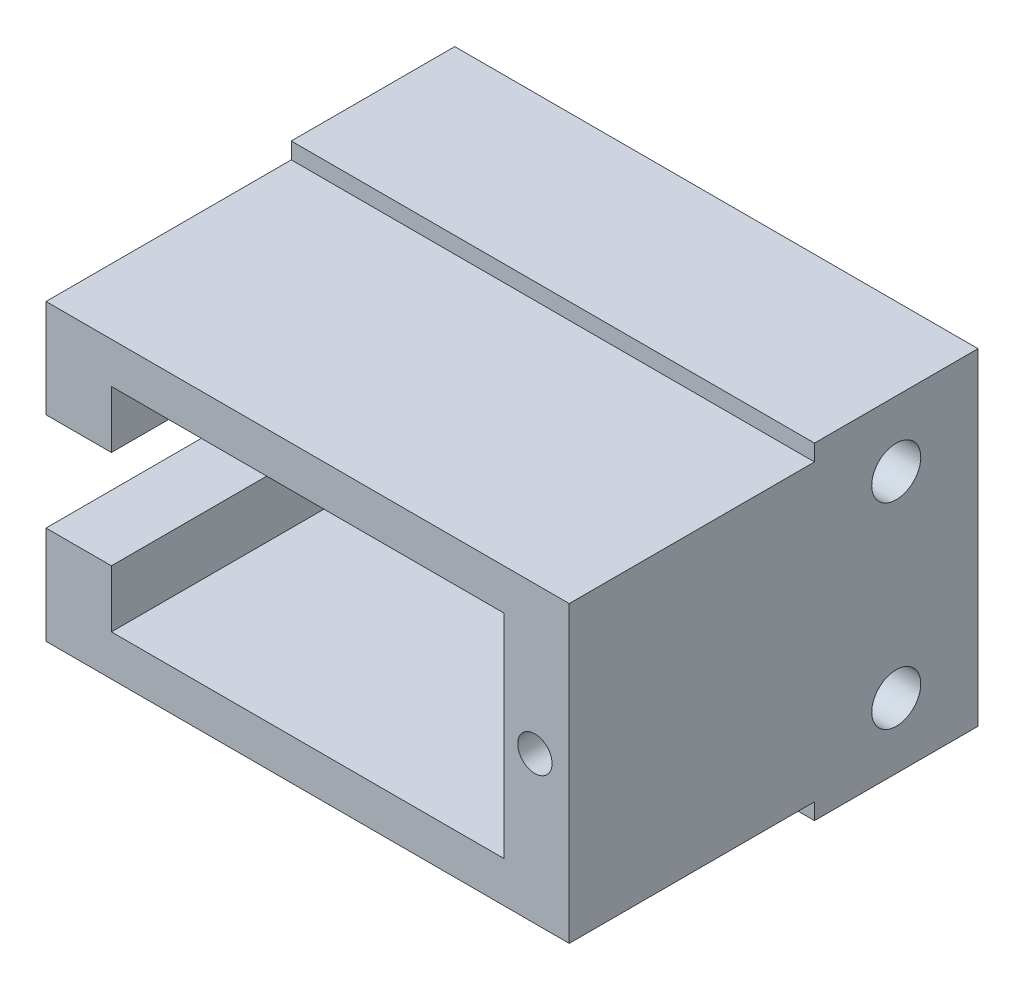
SolidWorks part; units mm, degrees
ref_plane "Plan de face" through (0, 0, 0) normal (0, 0, 1) x (1, 0, 0)
ref_plane "Plan de dessus" through (0, 0, 0) normal (0, 1, 0) x (1, 0, 0)
ref_plane "Plan de droite" through (0, 0, 0) normal (1, 0, 0) x (0, 0, -1)
sketch "Esquisse15" plane through (0, 0, 0) normal (0, 0, 1) x (1, 0, 0)
  line L1 (-16, 10) -> (16, 10)
  line L2 (-16, 10) -> (-16, -10)
  line L3 (-16, -10) -> (16, -10)
  line L4 (16, 10) -> (16, -10)
  line L5 (-16, 10) -> (16, -10) construction
  line L6 (-16, -10) -> (16, 10) construction
  point P0 (0, 0)
  dimension "D1" = 20
  dimension "D2" = 32
extrude "Boss.-Extru.1" add sketch "Esquisse15" along normal blind 10
sketch "Esquisse16" plane through (0, 0, 10) normal (0, 0, 1) x (1, 0, 0)
  line L0 (-16, 9) -> (16, 9)
  line L1 (-16, 10) -> (-16, -10) construction
  line L2 (16, -10) -> (16, 10) construction
  line L3 (16, 9) -> (16, -9)
  line L4 (16, -9) -> (-16, -9)
  line L5 (-16, -9) -> (-16, 9)
  line L6 (16, 10) -> (-16, 10) construction
  line L7 (-16, -10) -> (16, -10) construction
  line L9 (-12, 6.5) -> (12, 6.5)
  line L10 (-12, 6.5) -> (-12, -6.5)
  line L11 (-12, -6.5) -> (12, -6.5)
  line L12 (12, 6.5) -> (12, -6.5)
  line L13 (-12, 6.5) -> (12, -6.5) construction
  line L14 (-12, -6.5) -> (12, 6.5) construction
  point P12 (0, 0)
  dimension "D1" = 1
  dimension "D2" = 1
  dimension "D3" = 2.5
  dimension "D4" = 4
extrude "Boss.-Extru.2" add sketch "Esquisse16" along normal blind 15
sketch "Esquisse17" plane through (-16, 0, 0) normal (-1, 0, 0) x (0, 0, 1)
  line L0 (0, 3) -> (25, 3)
  line L1 (0, 10) -> (0, -10) construction
  line L2 (25, 3) -> (25, -3)
  line L3 (25, -3) -> (0, -3)
  line L4 (0, -3) -> (0, 3)
  point P5 (0, 0)
  dimension "D1" = 25
  dimension "D2" = 6
extrude "Enlèv. mat.-Extru.8" cut sketch "Esquisse17" against normal blind 4
sketch "Esquisse19" plane through (0, 0, 25) normal (0, 0, 1) x (1, 0, 0)
  line L5 (12, 0) -> (16, 0) construction
  line L6 (12, -6.5) -> (12, 6.5) construction
  line L7 (16, -9) -> (16, 9) construction
  line L12 (12, -6.5) -> (12, 6.5) construction
  circle A1 centre (13.9, 0) radius 1.05
  dimension "D2" = 2.1
  dimension "D4" = 1.9
extrude "Enlèv. mat.-Extru.10" cut sketch "Esquisse19" against normal blind 6
sketch "Esquisse20" plane through (16, 0, 0) normal (1, 0, 0) x (0, 0, -1)
  line L0 (-5, 10) -> (-5, -10) construction
  line L1 (-10, 10) -> (0, 10) construction
  line L2 (-10, -10) -> (0, -10) construction
  circle A0 centre (-5, 6) radius 1.5
  circle A1 centre (-5, -6) radius 1.5
  dimension "D1" = 3
  dimension "D2" = 3
  dimension "D4" = 4
  dimension "D3" = 4
extrude "Enlèv. mat.-Extru.11" cut sketch "Esquisse20" against normal blind 20
